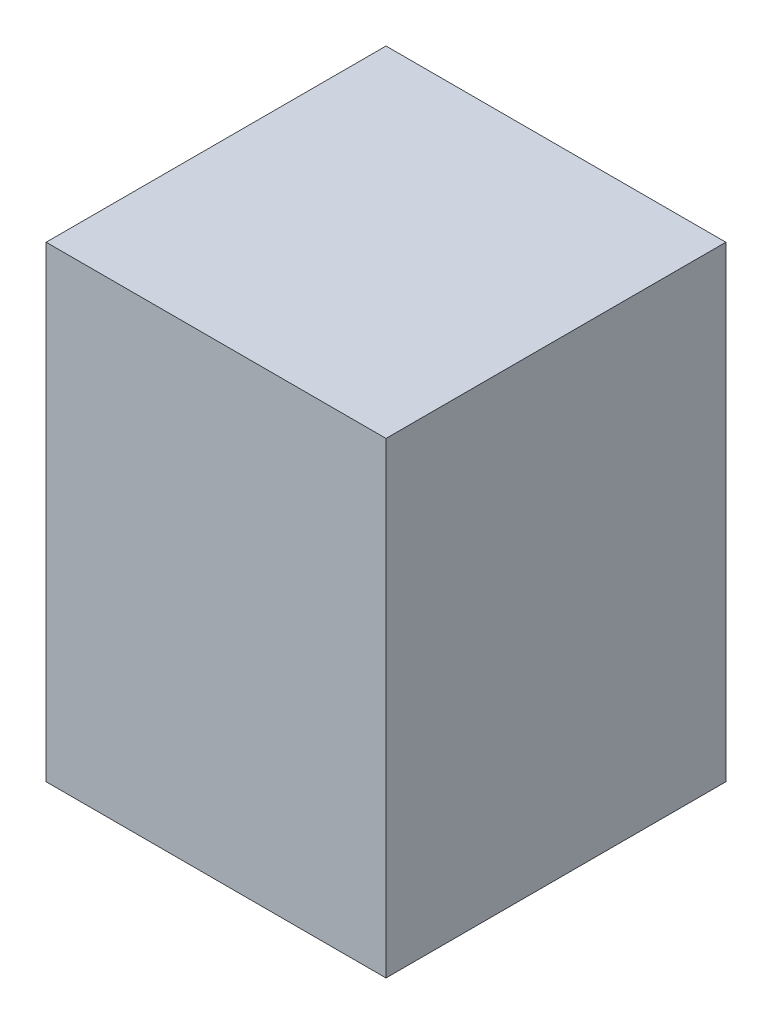
SolidWorks part; units mm, degrees
ref_plane "Alzado" through (0, 0, 0) normal (0, 0, 1) x (1, 0, 0)
ref_plane "Planta" through (0, 0, 0) normal (0, 1, 0) x (1, 0, 0)
ref_plane "Vista lateral" through (0, 0, 0) normal (1, 0, 0) x (0, 0, -1)
sketch "Croquis1" plane through (0, 0, 0) normal (0, 0, 1) x (1, 0, 0)
  line L1 (0, 0) -> (800, 0)
  line L2 (0, 0) -> (0, 1100)
  line L3 (0, 1100) -> (800, 1100)
  line L4 (800, 0) -> (800, 1100)
  dimension "D1" = 800
  dimension "D2" = 1100
extrude "Saliente-Extruir1" add sketch "Croquis1" along normal blind 800
